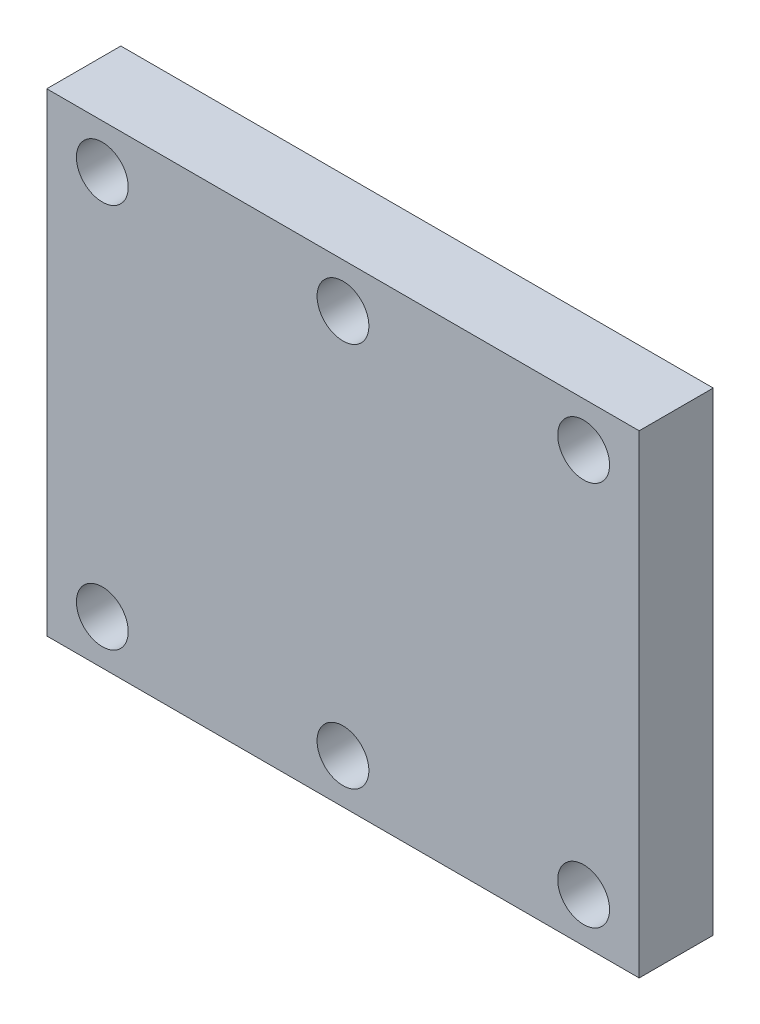
SolidWorks part; units mm, degrees
material "1.0545 (S355N)"
ref_plane "Front Plane" through (0, 0, 0) normal (0, 0, 1) x (1, 0, 0)
ref_plane "Top Plane" through (0, 0, 0) normal (0, 1, 0) x (1, 0, 0)
ref_plane "Right Plane" through (0, 0, 0) normal (1, 0, 0) x (0, 0, -1)
sketch "Sketch1" plane through (0, 0, 0) normal (0, 0, 1) x (1, 0, 0)
  line L0 (-79.4339, 0) -> (75.3991, 0) construction
  line L1 (0, 32) -> (80, 32)
  line L2 (0, 32) -> (0, -32)
  line L3 (0, -32) -> (80, -32)
  line L4 (80, 32) -> (80, -32)
  dimension "D1" = 64
  dimension "D2" = 80
extrude "Boss-Extrude1" add sketch "Sketch1" along normal blind 10
sketch "Sketch2" plane through (0, 0, 10) normal (0, 0, 1) x (1, 0, 0)
  line L1 (0, 32) -> (0, -32) construction
  point P0 (7.5, -26)
  dimension "D1" = 26
  dimension "D2" = 7.5
hole_wizard "M6 Clearance Hole1" positions "Sketch3" profile "Sketch4" hole size "M6" standard "ISO"
sketch "Sketch3" plane through (0, 0, 10) normal (0, 0, 1) x (1, 0, 0)
  point P0 (7.5, -26)
sketch "Sketch4" plane through (7.5, -26, 10) normal (1, 0, 0) x (0, -1, 0)
  line L0 (0, 0) -> (0, 28.103)
  line L1 (0, 28.103) -> (3.5, 26)
  line L2 (3.5, 26) -> (3.5, 0)
  line L5 (3.5, 0) -> (0, 0)
  line L10 (0, 28.103) -> (-3.5, 26) construction
  line L11 (0, -6.35) -> (0, 107.95) construction
  dimension "Hole Dia." = 7
  dimension "Hole Depth" = 26
  dimension "Drill Angle" = 118
pattern_linear "LPattern1" count 3 spacing 32.5 along (1, 0, 0) count 2 spacing 52 along (0, 1, 0) of "M6 Clearance Hole1"
